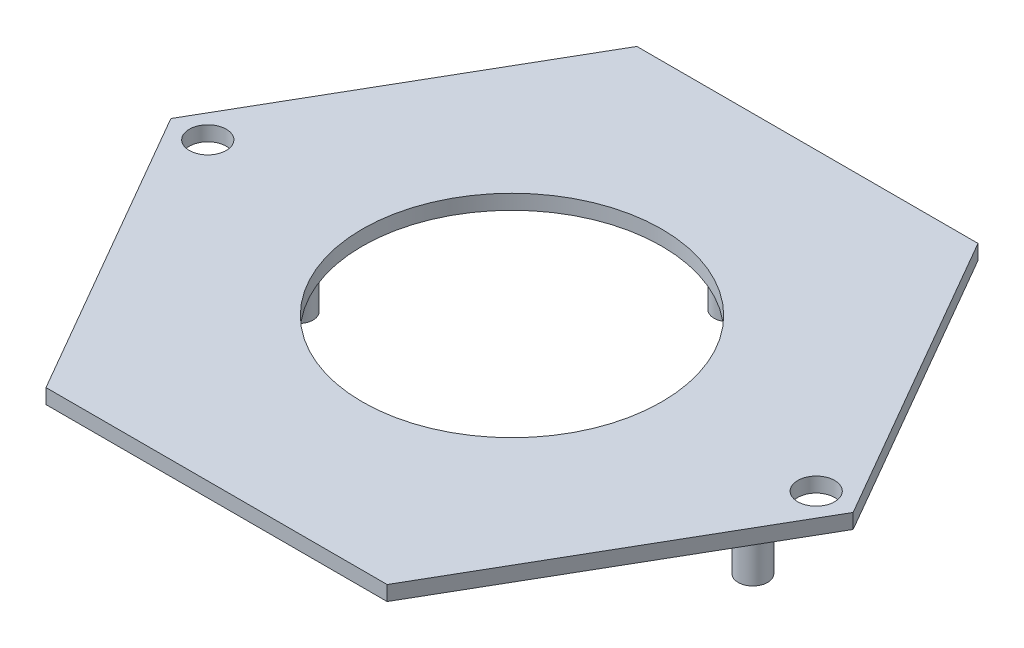
SolidWorks part; units mm, degrees
ref_plane "Front Plane" through (0, 0, 0) normal (0, 0, 1) x (1, 0, 0)
ref_plane "Top Plane" through (0, 0, 0) normal (0, 1, 0) x (1, 0, 0)
ref_plane "Right Plane" through (0, 0, 0) normal (1, 0, 0) x (0, 0, -1)
sketch "Sketch1" plane through (0, 0, 0) normal (0, 1, 0) x (1, 0, 0)
  line L1 (23.094, 0) -> (11.547, 20)
  line L2 (11.547, 20) -> (-11.547, 20)
  line L3 (-11.547, 20) -> (-23.094, 0)
  line L4 (-23.094, 0) -> (-11.547, -20)
  line L5 (-11.547, -20) -> (11.547, -20)
  line L6 (11.547, -20) -> (23.094, 0)
  circle A0 centre (0, 0) radius 20 construction
  dimension "D1" = 40
extrude "Boss-Extrude1" add sketch "Sketch1" along normal blind 1
sketch "Sketch3" plane through (0, 0, 0) normal (0, -1, 0) x (1, 0, 0)
  circle A0 centre (16.3082, 0) radius 1
  circle A1 centre (-14.4622, 0) radius 1
  circle A2 centre (0, -14.675) radius 1
  dimension "D1" = 2
  dimension "D2" = 2
  dimension "D3" = 2
extrude "Boss-Extrude2" add sketch "Sketch3" along normal blind 6
sketch "Sketch4" plane through (0, 1, 0) normal (0, 1, 0) x (1, 0, 0)
  circle A0 centre (0, 0) radius 10.1353
extrude "Cut-Extrude1" cut sketch "Sketch4" against normal blind 6
extrude "Cut-Extrude2" cut sketch "Sketch5" against normal blind 15
sketch "Sketch5" plane through (19.3711, 1, -19.3686) normal (0, 1, 0) x (-1, 0, 0)
  line L0 (-3.7229, 19.3686) -> (42.4651, 19.3686) construction
  circle A0 centre (-1.2229, 19.3686) radius 1.25
  circle A1 centre (39.9651, 19.3686) radius 1.25
